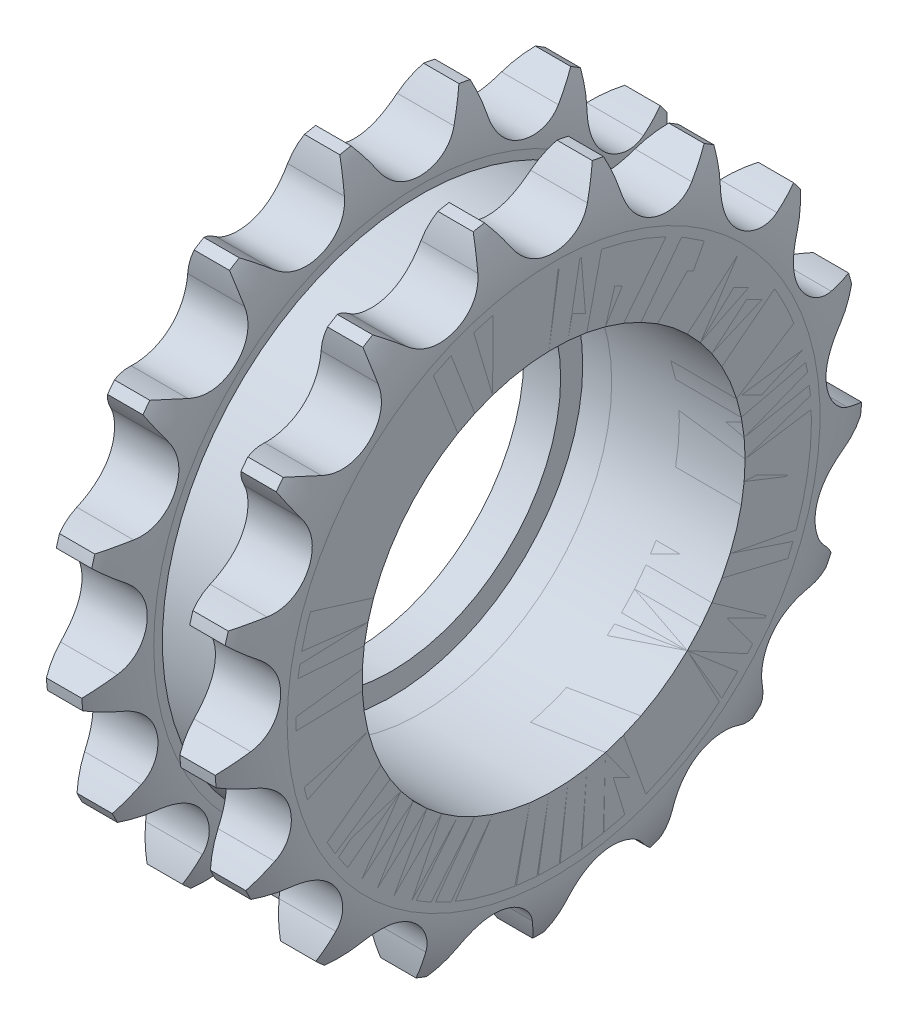
SolidWorks part; units mm, degrees
material "AISI 1045 钢，冷拔"
ref_plane "前视基准面" through (0, 0, 0) normal (0, 0, 1) x (1, 0, 0)
ref_plane "上视基准面" through (0, 0, 0) normal (0, 1, 0) x (1, 0, 0)
ref_plane "右视基准面" through (0, 0, 0) normal (1, 0, 0) x (0, 0, -1)
sketch "草图1" plane through (0, 0, 0) normal (1, 0, 0) x (0, 0, -1)
  line L0 (0, 0) -> (0, 58.3836) construction
  line L1 (0, 0) -> (22.6332, 58.4231) construction
  line L2 (0, 43.1975) -> (41.6385, 19.1575) construction
  line L3 (15.6047, 40.2804) -> (-27.7331, 33.5532) construction
  line L4 (0, 37.1975) -> (0, 0)
  line L5 (0, 0) -> (13.4373, 34.6856)
  circle A0 centre (0, 0) radius 43.1975 construction
  arc A1 (0, 37.1975) -> (5.1962, 40.1974) centre (0, 43.1975) ccw
  arc A2 (9.6757, 39.3601) -> (13.4373, 34.6856) centre (15.6047, 40.2804) ccw
  arc A3 (8.8473, 43.1013) -> (7.3201, 43.3868) centre (0, 0) ccw
  arc A4 (9.6757, 39.3601) -> (8.8473, 43.1013) centre (-19.9692, 34.7583) ccw
  arc A5 (7.3201, 43.3868) -> (5.1962, 40.1974) centre (31.1769, 25.1974) ccw
  dimension "D1" = 86.3949
  dimension "D3" = 12
  dimension "D4" = 12
  dimension "D5" = 88
  dimension "D8" = 60
  dimension "D9" = 60
  dimension "D2" = 21.176
  dimension "D6" = 60
  dimension "D7" = 60
extrude "凸台-拉伸1" add sketch "草图1" along normal blind 8.93
pattern_circular "阵列(圆周)1" count 17 over 360 about axis through (0, 0, 0) along (1, 0, 0) of "凸台-拉伸1"
sketch "草图2" plane through (0, 0, 0) normal (0, 0, 1) x (1, 0, 0)
  line L0 (0, 0) -> (0, 44) construction
  line L1 (0, 44) -> (8.93, 44) construction
  line L2 (0, 0) -> (8.93, 0) construction
  line L3 (8.93, -1.465) -> (8.93, 8.8829) construction
  line L4 (8.93, 0) -> (8.93, 44) construction
  line L5 (2.0638, 44) -> (2.0638, 0) construction
  line L6 (6.8663, 44) -> (6.8663, 0) construction
  line L7 (2.0638, 44) -> (6.8663, 44)
  line L8 (0, 36.1728) -> (0, 48.3528)
  line L9 (0, 48.3528) -> (8.93, 48.3528)
  line L10 (8.93, 48.3528) -> (8.93, 36.1728)
  arc A0 (2.0638, 44) -> (0, 36.1728) centre (15.875, 36.1728) ccw
  arc A1 (8.93, 36.1728) -> (6.8663, 44) centre (-6.945, 36.1728) ccw
  dimension "D4" = 31.75
  dimension "D5" = 31.75
  dimension "D1" = 44
  dimension "D2" = 2.0638
  dimension "D3" = 2.0638
revolve "切除-旋转1" cut sketch "草图2" angle 360 about L2
sketch "草图4" plane through (8.93, 0, 0) normal (1, 0, 0) x (0, 0, -1)
  circle A0 centre (0, 0) radius 35
  dimension "D1" = 70
extrude "凸台-拉伸3" add sketch "草图4" along normal blind 18.11 separate body
pattern_linear "阵列(线性)1" count 2 spacing 18.11 along (1, 0, 0) of "阵列(圆周)1"
sketch "草图5" plane through (27.04, 0, 0) normal (1, 0, 0) x (0, 0, -1)
  circle A0 centre (0, 0) radius 26
  dimension "D1" = 52
extrude "切除-拉伸1" cut sketch "草图5" against normal offset from surface (22.04 mm away) 5 up to face at (0, 0, 36.1728)
sketch "草图6" plane through (5, 0, 0) normal (1, 0, 0) x (0, 0, -1)
  circle A0 centre (0, 0) radius 23
  dimension "D1" = 46
extrude "切除-拉伸2" cut sketch "草图6" against normal up to next (5 mm away)
